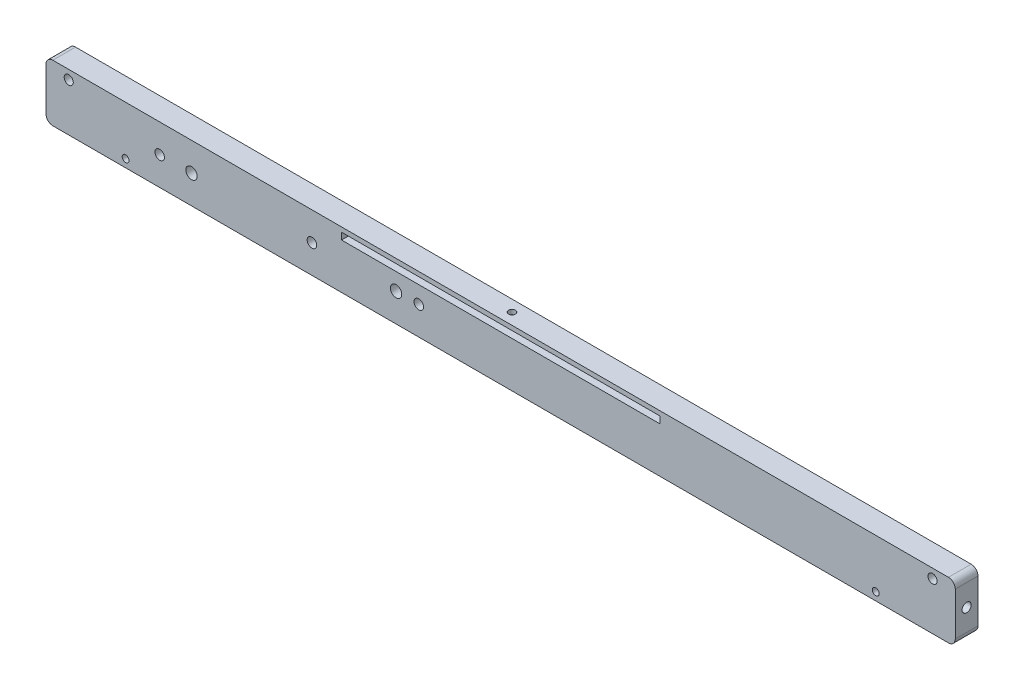
SolidWorks part; units mm, degrees
ref_plane "前视基准面" through (0, 0, 0) normal (0, 0, 1) x (1, 0, 0)
ref_plane "上视基准面" through (0, 0, 0) normal (0, 1, 0) x (1, 0, 0)
ref_plane "右视基准面" through (0, 0, 0) normal (1, 0, 0) x (0, 0, -1)
other "Configuration Table"
sketch "草图1" plane through (0, 0, 0) normal (0, 0, 1) x (1, 0, 0)
  line L1 (-197, 12.5) -> (197, 12.5)
  line L2 (-200, 9.5) -> (-200, -9.5)
  line L3 (-197, -12.5) -> (197, -12.5)
  line L4 (200, 9.5) -> (200, -9.5)
  line L5 (-200, 12.5) -> (200, -12.5) construction
  line L6 (-200, -12.5) -> (200, 12.5) construction
  arc A0 (197, -12.5) -> (200, -9.5) centre (197, -9.5) ccw
  arc A1 (197, 12.5) -> (200, 9.5) centre (197, 9.5) cw
  arc A2 (-200, -9.5) -> (-197, -12.5) centre (-197, -9.5) ccw
  arc A3 (-197, 12.5) -> (-200, 9.5) centre (-197, 9.5) ccw
  point P0 (0, 0)
  dimension "D3" = 3
  dimension "D1" = 400
  dimension "D2" = 25
extrude "凸台-拉伸1" add sketch "草图1" against normal blind 10
sketch "草图3" plane through (0, 0, 0) normal (0, 0, 1) x (1, 0, 0)
  line L0 (-70, 10.5) -> (70, 10.5)
  line L1 (-200, 9.5) -> (-200, -9.5) construction
  line L2 (200, -9.5) -> (200, 9.5) construction
  line L3 (70, 10.5) -> (70, 7.5)
  line L4 (197, 12.5) -> (-197, 12.5) construction
  line L6 (-70, 10.5) -> (-70, 7.5)
  line L7 (-70, 7.5) -> (70, 7.5)
  dimension "D1" = 130
  dimension "D2" = 2
  dimension "D3" = 3
  dimension "D4" = 130
extrude "切除-拉伸1" cut sketch "草图3" against normal blind 10
sketch "草图4" plane through (0, 0, 0) normal (0, 0, 1) x (1, 0, 0)
  line L0 (-200, 8.5) -> (200, 8.5)
  line L1 (-200, 9.5) -> (-200, -9.5) construction
  line L2 (200, -9.5) -> (200, 9.5) construction
  line L3 (190, 12.5) -> (190, -12.5)
  line L4 (197, 12.5) -> (-197, 12.5) construction
  line L5 (-197, -12.5) -> (197, -12.5) construction
  line L6 (-190, 12.5) -> (-190, -12.5)
  circle A0 centre (190, 8.5) radius 2
  circle A1 centre (-190, 8.5) radius 2
  point P14 (-190, 8.5)
  point P15 (190, 8.5)
  dimension "D4" = 4
  dimension "D5" = 4
  dimension "D1" = 4
  dimension "D2" = 10
  dimension "D3" = 10
extrude "切除-拉伸2" cut sketch "草图4" against normal blind 10 contours L6 A1 L0 | L0 A1 L6 | L0 A1 L6 | L6 A1 L0 | L0 A0 L3 | L3 A0 L0 | L0 A0 L3 | L3 A0 L0
sketch "草图5" plane through (0, 0, 0) normal (0, 0, 1) x (1, 0, 0)
  line L0 (-150, 12.5) -> (-150, -12.5) construction
  line L1 (-200, 9.5) -> (-200, -9.5) construction
  line L2 (200, -9.5) -> (200, 9.5) construction
  line L4 (-200, 0) -> (200, 0) construction
  line L5 (197, 12.5) -> (-197, 12.5) construction
  line L6 (-197, -12.5) -> (197, -12.5) construction
  line L7 (-83, 12.5) -> (-83, -12.8654) construction
  line L8 (-36, 12.5) -> (-36, -12.5) construction
  line L9 (-136, 12.5) -> (-136, -12.5) construction
  line L10 (-46, 12.5) -> (-46, -12.5) construction
  point P16 (-150, 0)
  point P17 (-83, 0)
  point P18 (-36, 0)
  point P21 (-136, 0)
  dimension "D1" = 50
  dimension "D2" = 67
  dimension "D3" = 47
  dimension "D4" = 14
  dimension "D5" = 10
hole_wizard "M5 螺纹孔3" positions "草图6" profile "草图7" tap size "M5" standard "GB"
sketch "草图6" plane through (0, 0, 0) normal (0, 0, 1) x (1, 0, 0)
  point P0 (-150, 0)
  point P3 (-83, 0)
  point P6 (-36, 0)
cosmetic thread "孔螺蚊线1" parameters "D1"=10, "D2"=5
cosmetic thread "孔螺蚊线2" parameters "D1"=10, "D2"=5
cosmetic thread "孔螺蚊线3" parameters "D1"=10, "D2"=5
sketch "草图7" plane through (-150, 0, 0) normal (1, 0, 0) x (0, -1, 0)
  line L0 (0, 0) -> (0, 15.2618)
  line L1 (0, 15.2618) -> (2.1, 14)
  line L2 (2.1, 14) -> (2.1, 0)
  line L5 (2.1, 0) -> (0, 0)
  line L10 (0, 15.2618) -> (-2.1, 14) construction
  line L11 (0, -6.35) -> (0, 107.95) construction
  dimension "螺纹孔钻头直径" = 4.2
  dimension "螺纹孔钻头深度" = 14
  dimension "导头角度" = 118
hole_wizard "M6 螺纹孔2" positions "草图8" profile "草图9" tap size "M6" standard "GB"
sketch "草图8" plane through (0, 0, 0) normal (0, 0, 1) x (1, 0, 0)
  line L0 (-46, 12.5) -> (-46, -12.5) construction
  point P0 (-46, 0)
  point P5 (-136, 0)
sketch "草图9" plane through (-46, 0, 0) normal (1, 0, 0) x (0, -1, 0)
  line L0 (0, 0) -> (0, 18.5022)
  line L1 (0, 18.5022) -> (2.5, 17)
  line L2 (2.5, 17) -> (2.5, 0)
  line L5 (2.5, 0) -> (0, 0)
  line L10 (0, 18.5022) -> (-2.5, 17) construction
  line L11 (0, -6.35) -> (0, 107.95) construction
  dimension "螺纹孔钻头直径" = 5
  dimension "螺纹孔钻头深度" = 17
  dimension "导头角度" = 118
cosmetic thread "孔螺蚊线4" parameters "D1"=12, "D2"=6
cosmetic thread "孔螺蚊线5" parameters "D1"=12, "D2"=6
sketch "草图10" plane through (0, -12.5, 0) normal (0, -1, 0) x (1, 0, 0)
  line L0 (-200, -5) -> (200, -5)
  line L1 (-200, -10) -> (-200, 0) construction
  line L2 (200, -10) -> (200, 0) construction
  line L3 (165, 0) -> (165, -10)
  line L4 (-200, 0) -> (200, 0) construction
  line L5 (-197, -10) -> (197, -10) construction
  line L6 (-165, 0) -> (-165, -10)
  line L9 (150, -2.5) -> (180, -2.5)
  line L10 (150, -2.5) -> (150, -7.5)
  line L11 (150, -7.5) -> (180, -7.5)
  line L12 (180, -2.5) -> (180, -7.5)
  line L13 (150, -2.5) -> (180, -7.5) construction
  line L14 (150, -7.5) -> (180, -2.5) construction
  line L15 (-180, -2.5) -> (-150, -2.5)
  line L16 (-180, -2.5) -> (-180, -7.5)
  line L17 (-180, -7.5) -> (-150, -7.5)
  line L18 (-150, -2.5) -> (-150, -7.5)
  line L19 (-180, -2.5) -> (-150, -7.5) construction
  line L20 (-180, -7.5) -> (-150, -2.5) construction
  point P14 (-165, -5)
  point P17 (165, -5)
  point P18 (165, -5)
  point P23 (-165, -5)
  dimension "D1" = 35
  dimension "D2" = 35
  dimension "D3" = 30
  dimension "D4" = 5
  dimension "D5" = 30
  dimension "D6" = 5
extrude "切除-拉伸3" cut sketch "草图10" against normal blind 7 contours L15 L16 L0 L6 | L18 L15 L6 L0 | L18 L0 L6 L17 | L16 L17 L6 L0 | L9 L10 L0 L3 | L12 L9 L3 L0 | L10 L11 L3 L0 | L12 L0 L3 L11
sketch "草图11" plane through (0, 0, 0) normal (0, 0, 1) x (1, 0, 0)
  line L0 (-200, -9) -> (200, -9) construction
  line L1 (-200, 9.5) -> (-200, -9.5) construction
  line L2 (200, -9.5) -> (200, 9.5) construction
  line L3 (165, 12.5) -> (165, -12.5) construction
  line L4 (197, 12.5) -> (-197, 12.5) construction
  line L5 (-197, -12.5) -> (197, -12.5) construction
  line L6 (-165, 12.5) -> (-165, -12.5) construction
  circle A1 centre (-165, -9) radius 1.5
  circle A2 centre (165.0016, -9) radius 1.5
  point P14 (-165, -9)
  point P15 (165.0016, -9)
  point P21 (165, -9)
  dimension "D4" = 3
  dimension "D1" = 35
  dimension "D2" = 35
  dimension "D3" = 3.5
extrude "切除-拉伸4" cut sketch "草图11" against normal through all
sketch "草图12" plane through (0, 0, 0) normal (0, 0, 1) x (1, 0, 0)
  text T0 "不吃西瓜" font "华文行楷" height 3.5
sketch "草图13" plane through (200, 0, 0) normal (1, 0, 0) x (0, 0, -1)
  line L0 (0, 0) -> (10, 0) construction
  line L1 (10, -9.5) -> (10, 9.5) construction
  line L2 (5, 12.5) -> (5, -12.5) construction
  line L5 (10, 12.5) -> (0, 12.5) construction
  line L6 (10, -12.5) -> (0, -12.5) construction
  circle A0 centre (5, 0) radius 2
  point P11 (5, 0)
  dimension "D1" = 4
extrude "切除-拉伸6" cut sketch "草图13" against normal blind 5
sketch "草图14" plane through (-200, 0, 0) normal (-1, 0, 0) x (0, 0, 1)
  line L0 (-10.1144, 0) -> (0, 0) construction
  line L1 (-5, 12.5) -> (-5, -12.5) construction
  line L2 (-10, 12.5) -> (0, 12.5) construction
  line L3 (-10, -12.5) -> (0, -12.5) construction
  circle A0 centre (-5, 0) radius 2
  point P9 (-5, 0)
  dimension "D1" = 4
extrude "切除-拉伸7" cut sketch "草图14" against normal blind 5
sketch "草图16" plane through (0, 12.5, 0) normal (0, 1, 0) x (1, 0, 0)
  line L0 (0, 10) -> (0, 0) construction
  line L1 (197, 10) -> (-197, 10) construction
  line L2 (-200, 5) -> (200, 5) construction
  line L3 (-200, 10) -> (-200, 0) construction
  line L4 (200, 10) -> (200, 0) construction
  circle A0 centre (0, 5) radius 1.5
  point P11 (0, 5)
  dimension "D1" = 3
extrude "切除-拉伸8" cut sketch "草图16" against normal blind 10
